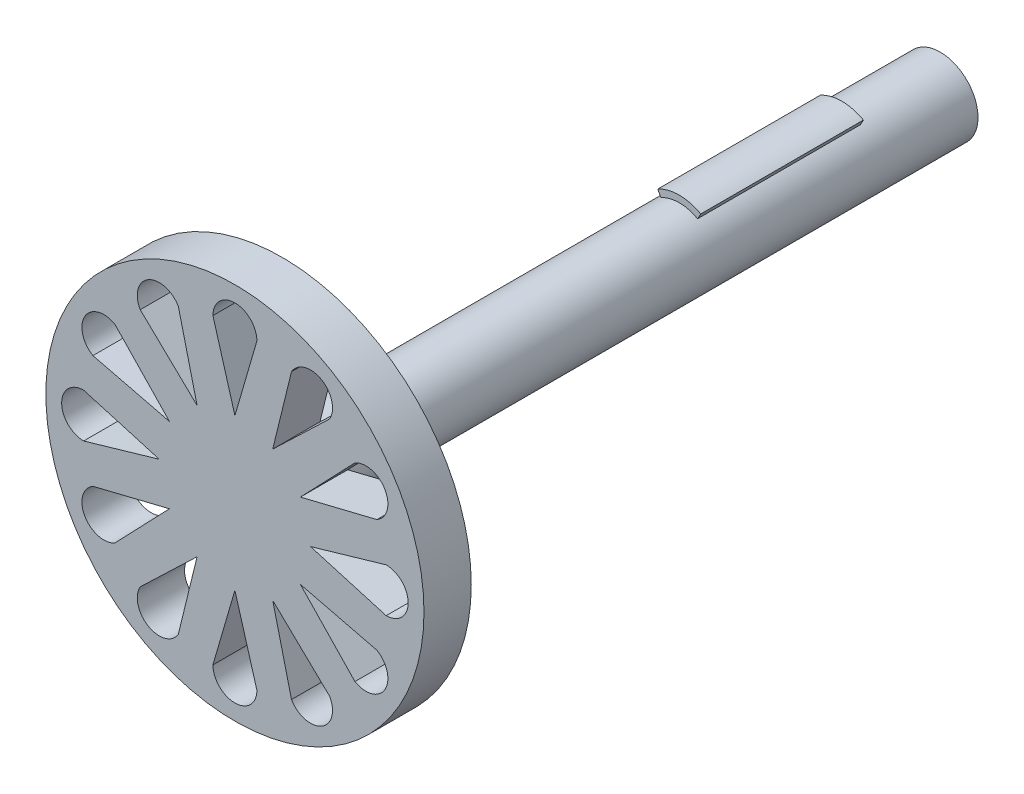
SolidWorks part; units mm, degrees
ref_plane "Front Plane" through (0, 0, 0) normal (0, 0, 1) x (1, 0, 0)
ref_plane "Top Plane" through (0, 0, 0) normal (0, 1, 0) x (1, 0, 0)
ref_plane "Right Plane" through (0, 0, 0) normal (1, 0, 0) x (0, 0, -1)
sketch "Sketch3" plane through (0, 0, 0) normal (0, 0, 1) x (1, 0, 0)
  circle A0 centre (0, 0) radius 2
  dimension "D1" = 4
extrude "Boss-Extrude1" add sketch "Sketch3" along normal blind 5.2
sketch "Sketch4" plane through (0, 0, 5.2) normal (0, 0, 1) x (1, 0, 0)
  line L0 (0, 0) -> (-1.1393, 2.0554)
  line L1 (0, 0) -> (0, 2.35)
  line L2 (0, 0) -> (1.1393, 2.0554)
  arc A0 (1.1393, 2.0554) -> (-1.1393, 2.0554) centre (0, 0) ccw
  circle A2 centre (0, 0) radius 2
  circle M5 centre (0, 0) radius 2
  dimension "D1" = 2.35
  dimension "D2" = 29
extrude "Boss-Extrude2" add sketch "Sketch4" along normal blind 8.6 contours L2 A0 L0 M5 | L0 L2 M5 | L2 L0 M5
sketch "Sketch5" plane through (0, 0, 13.8) normal (0, 0, 1) x (1, 0, 0)
  circle A0 centre (0, 0) radius 2
extrude "Boss-Extrude3" add sketch "Sketch5" along normal blind 15
sketch "Sketch7" plane through (0, 0, 28.8) normal (0, 0, 1) x (1, 0, 0)
  circle A0 centre (0, 0) radius 2
  dimension "D1" = 4
extrude "Boss-Extrude4" add sketch "Sketch7" along normal blind 6
sketch "Sketch8" plane through (0, 0, 34.8) normal (0, 0, 1) x (1, 0, 0)
  circle A0 centre (0, 0) radius 10
  dimension "D1" = 20
extrude "Boss-Extrude5" add sketch "Sketch8" along normal blind 2.5
sketch "Sketch9" plane through (0, 0, 37.3) normal (0, 0, 1) x (1, 0, 0)
  line L1 (-9.1634, 0) -> (-8, 0) construction
  line L12 (7.5099, -2.9925) -> (3.4641, -2)
  line L15 (6.3465, -5.0075) -> (3.4641, -2)
  line L16 (-6.3465, 5.0075) -> (-3.4641, 2)
  line L17 (-7.5099, -2.9925) -> (-3.4641, -2)
  line L18 (-6.3465, -5.0075) -> (-3.4641, -2)
  line L19 (-7.5099, 2.9925) -> (-3.4641, 2)
  line L20 (6.3465, 5.0075) -> (3.4641, 2)
  line L21 (7.5099, 2.9925) -> (3.4641, 2)
  line L27 (-1.1634, -8) -> (0, -4)
  line L28 (1.1634, -8) -> (0, -4)
  line L29 (1.1634, 8) -> (0, 4)
  line L30 (-1.1634, 8) -> (0, 4)
  line L31 (-8, 1.1634) -> (-4, 0)
  line L32 (-8, -1.1634) -> (-4, 0)
  line L34 (8, -1.1634) -> (4, 0)
  line L35 (8, 1.1634) -> (4, 0)
  line L36 (-2.9925, 7.5099) -> (-2, 3.4641)
  line L37 (-5.0075, 6.3465) -> (-2, 3.4641)
  line L38 (5.0075, -6.3465) -> (2, -3.4641)
  line L39 (2.9925, -7.5099) -> (2, -3.4641)
  line L40 (2.9925, 7.5099) -> (2, 3.4641)
  line L41 (5.0075, 6.3465) -> (2, 3.4641)
  line L42 (-5.0075, -6.3465) -> (-2, -3.4641)
  line L43 (-2.9925, -7.5099) -> (-2, -3.4641)
  line L45 (9.1634, 0) -> (10, 0) construction
  circle A0 centre (0, 0) radius 10 construction
  arc A2 (7.5099, -2.9925) -> (6.3465, -5.0075) centre (6.9282, -4) cw
  arc A3 (-7.5099, -2.9925) -> (-6.3465, -5.0075) centre (-6.9282, -4) ccw
  arc A4 (-7.5099, 2.9925) -> (-6.3465, 5.0075) centre (-6.9282, 4) cw
  arc A5 (7.5099, 2.9925) -> (6.3465, 5.0075) centre (6.9282, 4) ccw
  arc A6 (1.1634, -8) -> (-1.1634, -8) centre (0, -8) cw
  arc A7 (1.1634, 8) -> (-1.1634, 8) centre (0, 8) ccw
  arc A8 (-8, 1.1634) -> (-8, -1.1634) centre (-8, 0) ccw
  arc A9 (8, 1.1634) -> (8, -1.1634) centre (8, 0) cw
  arc A10 (-5.0075, 6.3465) -> (-2.9925, 7.5099) centre (-4, 6.9282) cw
  arc A11 (2.9925, -7.5099) -> (5.0075, -6.3465) centre (4, -6.9282) ccw
  arc A12 (2.9925, 7.5099) -> (5.0075, 6.3465) centre (4, 6.9282) cw
  arc A13 (-5.0075, -6.3465) -> (-2.9925, -7.5099) centre (-4, -6.9282) ccw
  dimension "D3" = 4.1658
  dimension "D4" = 1.1634
  dimension "D1" = 4.1658
  dimension "D5" = 2.3268
extrude "Cut-Extrude1" cut sketch "Sketch9" against normal blind 12
